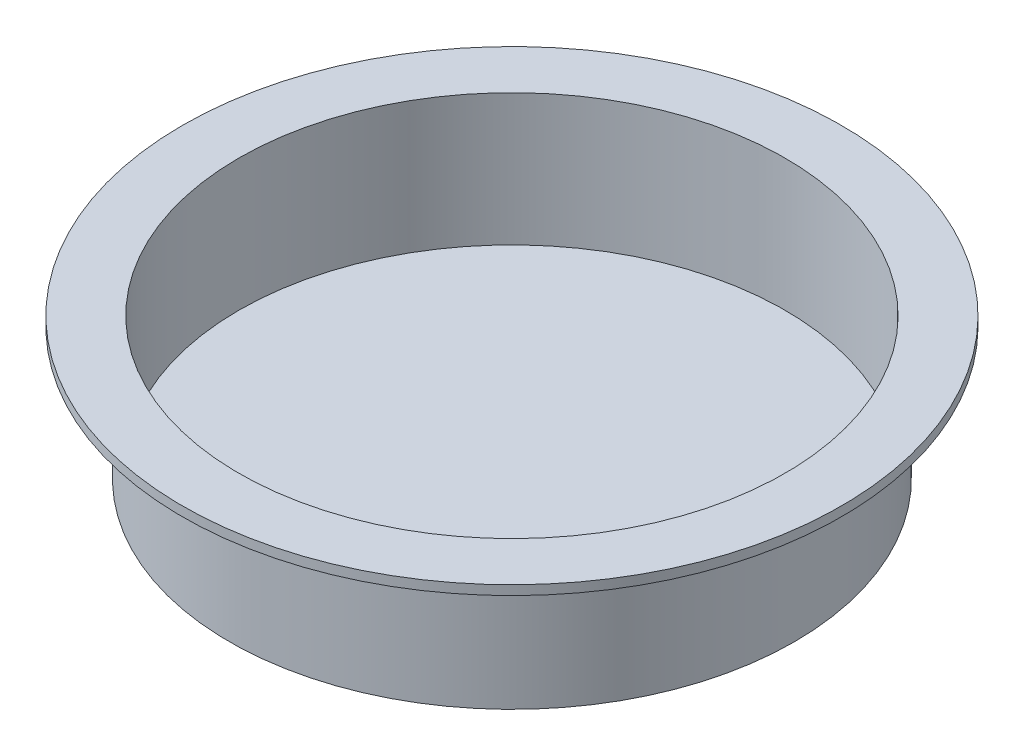
SolidWorks part; units mm, degrees
ref_plane "Front Plane" through (0, 0, 0) normal (0, 0, 1) x (1, 0, 0)
ref_plane "Top Plane" through (0, 0, 0) normal (0, 1, 0) x (1, 0, 0)
ref_plane "Right Plane" through (0, 0, 0) normal (1, 0, 0) x (0, 0, -1)
sketch "Sketch3" plane through (0, 0, 0) normal (0, 0, 1) x (1, 0, 0)
  line L0 (0, 0) -> (38.1, 0)
  line L1 (38.1, 0) -> (38.1, 17.78)
  line L2 (38.1, 17.78) -> (44.45, 17.78)
  line L3 (44.45, 17.78) -> (44.45, 19.05)
  line L4 (44.45, 19.05) -> (0, 19.05)
  line L5 (0, 19.05) -> (0, 0)
  dimension "D1" = 38.1
  dimension "D2" = 44.45
  dimension "D3" = 1.27
  dimension "D4" = 19.05
revolve "Revolve1" add sketch "Sketch3" angle 360 about L5
sketch "Sketch4" plane through (0, 19.05, 0) normal (0, 1, 0) x (1, 0, 0)
  circle A0 centre (0, 0) radius 36.83
  dimension "D1" = 73.66
extrude "Cut-Extrude1" cut sketch "Sketch4" against normal blind 17.78
